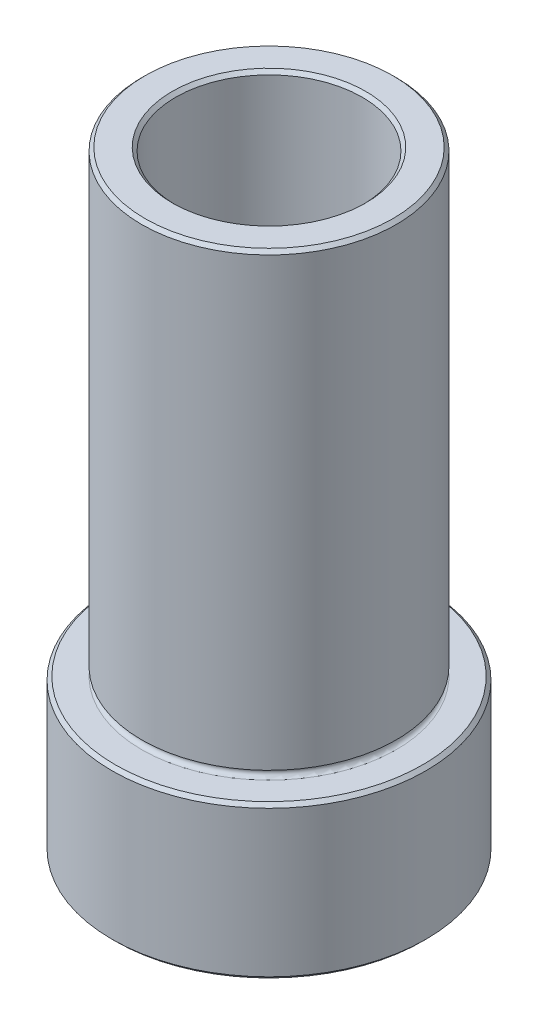
SolidWorks part; units mm, degrees
ref_plane "Vorne" through (0, 0, 0) normal (0, 0, 1) x (1, 0, 0)
ref_plane "Oben" through (0, 0, 0) normal (0, 1, 0) x (1, 0, 0)
ref_plane "Rechts" through (0, 0, 0) normal (1, 0, 0) x (0, 0, -1)
sketch "Skizze1" plane through (0, 0, 0) normal (0, 1, 0) x (1, 0, 0)
  circle A0 centre (0, 0) radius 9.25
  dimension "D1" = 18.5
extrude "Aufsatz-Linear austragen1" add sketch "Skizze1" along normal blind 9
sketch "Skizze2" plane through (0, 9, 0) normal (0, 1, 0) x (1, 0, 0)
  circle A0 centre (0, 0) radius 7.5
  dimension "D1" = 15
extrude "Aufsatz-Linear austragen2" add sketch "Skizze2" along normal blind 27
sketch "Skizze3" plane through (0, 0, 0) normal (0, -1, 0) x (1, 0, 0)
  circle A0 centre (0, 0) radius 5.5
  dimension "D1" = 11
extrude "Schnitt-Linear austragen1" cut sketch "Skizze3" against normal blind 40
chamfer "Fase1" distance 0.2 angle 45 5 edges at (0, 0, -5.5) (0, 36, 5.5) (0, 36, 7.5) (0, 0, 9.25) (0, 9, 9.25)
sketch "Skizze4" plane through (0, 0, 0) normal (1, 0, 0) x (0, 0, -1)
  line L0 (-7.5, 35.8) -> (-7.5, 9) construction
  line L1 (9.05, 9) -> (-9.05, 9) construction
  line L2 (0, 12.4928) -> (0, 9.25) construction
  line L3 (0, 4.95) -> (0, -4.95) construction
  circle A0 centre (-7.5, 9.25) radius 0.25
  dimension "D1" = 0.5
revolve "Schnitt-Rotation1" cut sketch "Skizze4" angle 360 about L2
